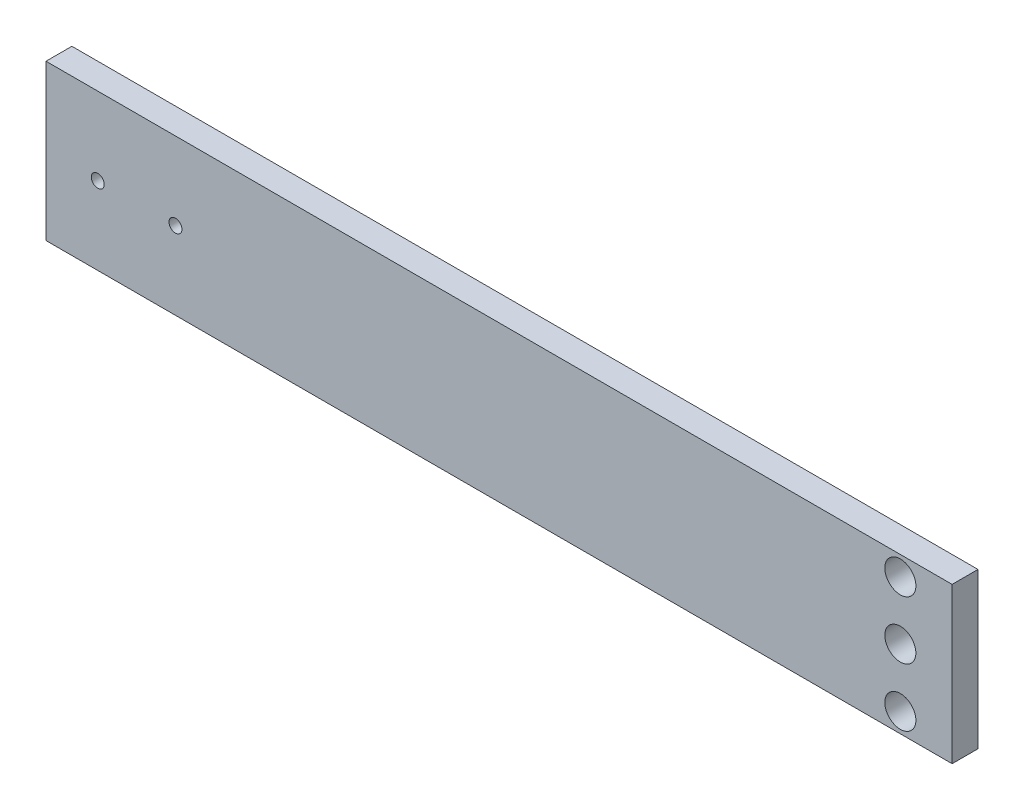
SolidWorks part; units mm, degrees
ref_plane "前视基准面" through (0, 0, 0) normal (0, 0, 1) x (1, 0, 0)
ref_plane "上视基准面" through (0, 0, 0) normal (0, 1, 0) x (1, 0, 0)
ref_plane "右视基准面" through (0, 0, 0) normal (1, 0, 0) x (0, 0, -1)
sketch "草图1" plane through (0, 0, 0) normal (0, 0, 1) x (1, 0, 0)
  line L1 (-175, 30) -> (175, 30)
  line L2 (-175, 30) -> (-175, -30)
  line L3 (-175, -30) -> (175, -30)
  line L4 (175, 30) -> (175, -30)
  line L5 (-175, 30) -> (175, -30) construction
  line L6 (-175, -30) -> (175, 30) construction
  point P0 (0, 0)
  dimension "D1" = 350
  dimension "D2" = 60
extrude "凸台-拉伸1" add sketch "草图1" along normal blind 10
sketch "草图2" plane through (0, 0, 10) normal (0, 0, 1) x (1, 0, 0)
  line L0 (-155, 0) -> (-125, 0)
  line L1 (-175, 30) -> (-175, -30) construction
  line L2 (155, 22.5) -> (155, -22.5)
  line L3 (175, -30) -> (175, 30) construction
  line L4 (-175, -30) -> (175, -30) construction
  point P7 (151.5551, 20.6494)
  point P12 (155, 0)
  dimension "D1" = 20
  dimension "D2" = 30
  dimension "D3" = 45
  dimension "D4" = 20
  dimension "D5" = 7.5
hole_wizard "M6 螺纹孔1" positions "3D草图1" profile "草图4" tap size "M6" standard "GB"
sketch3d "3D草图1"
  point P0 (-155, 0, 10)
  point P3 (-125, 0, 10)
sketch "草图4" plane through (-155, 0, 10) normal (1, 0, 0) x (0, -1, 0)
  line L0 (0, 0) -> (0, 21.5022)
  line L1 (0, 21.5022) -> (2.5, 20)
  line L2 (2.5, 20) -> (2.5, 0)
  line L5 (2.5, 0) -> (0, 0)
  line L10 (0, 21.5022) -> (-2.5, 20) construction
  line L11 (0, -6.35) -> (0, 107.95) construction
  dimension "螺纹孔钻头直径" = 5
  dimension "螺纹孔钻头深度" = 20
  dimension "导头角度" = 118
cosmetic thread "孔螺蚊线1" parameters "D1"=10, "D2"=6
cosmetic thread "孔螺蚊线2" parameters "D1"=10, "D2"=6
hole_wizard "大小mm 暗销槽口1" positions "草图7" profile "草图6" size "Ø12.0" standard "GB" slot yes
sketch "草图7" plane through (0, 0, 10) normal (0, 0, 1) x (1, 0, 0)
  point P0 (155, -22.5)
  point P3 (155, 0)
  point P6 (155, 22.5)
sketch "草图6" plane through (155, -22.5, 10) normal (1, 0, 0) x (0, -1, 0)
  line L0 (0, 0) -> (0, 23.6052)
  line L1 (0, 23.6052) -> (6, 20)
  line L2 (6, 20) -> (6, 0)
  line L5 (6, 0) -> (0, 0)
  line L10 (0, 23.6052) -> (-6, 20) construction
  line L11 (0, -6.35) -> (0, 107.95) construction
  dimension "孔直径" = 12
  dimension "孔深度" = 20
  dimension "导头角度" = 118
